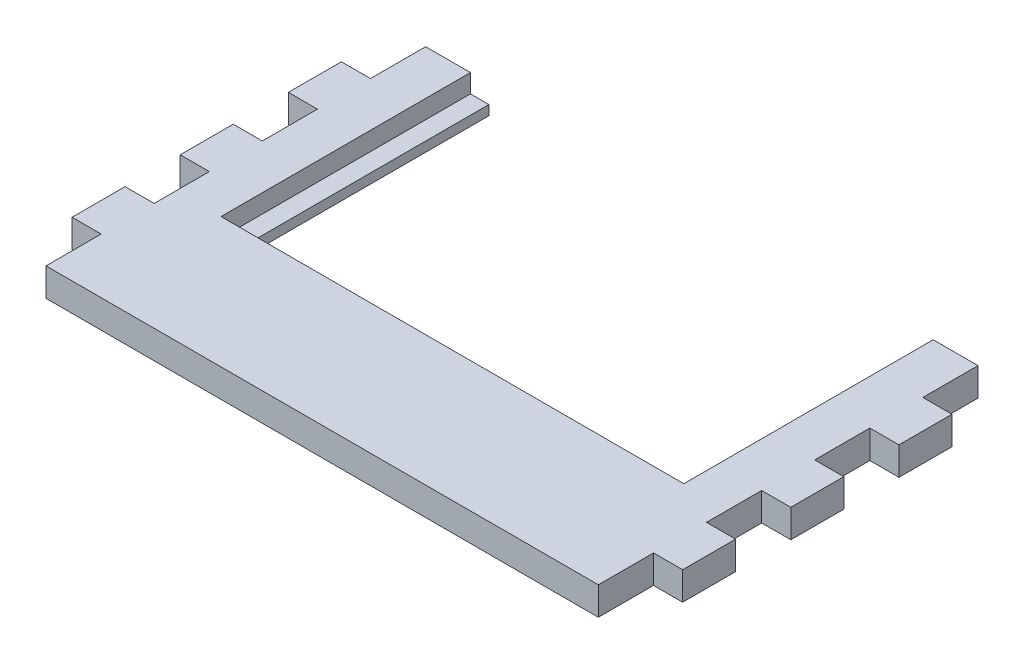
SolidWorks part; units mm, degrees
ref_plane "Plan de face" through (0, 0, 0) normal (0, 0, 1) x (1, 0, 0)
ref_plane "Plan de dessus" through (0, 0, 0) normal (0, 1, 0) x (1, 0, 0)
ref_plane "Plan de droite" through (0, 0, 0) normal (1, 0, 0) x (0, 0, -1)
sketch "Esquisse1" plane through (0, 0, 0) normal (0, 1, 0) x (1, 0, 0)
  line L1 (-163.0852, 185.3139) -> (167.4148, 185.3139)
  line L2 (-163.0852, 185.3139) -> (-163.0852, -20.1861)
  line L3 (-163.0852, -20.1861) -> (167.4148, -20.1861)
  line L4 (167.4148, 185.3139) -> (167.4148, -20.1861)
  line L5 (-113.0852, 185.3139) -> (117.4148, 185.3139)
  line L6 (-113.0852, 185.3139) -> (-113.0852, 60.3139)
  line L7 (-113.0852, 60.3139) -> (117.4148, 60.3139)
  line L8 (117.4148, 185.3139) -> (117.4148, 60.3139)
  dimension "D1" = 330.5
  dimension "D2" = 205.5
  dimension "D3" = 50
  dimension "D4" = 50
  dimension "D5" = 80.5
extrude "Boss.-Extru.1" add sketch "Esquisse1" along normal blind 15.25 contours L1 L8 L7 L6 L2 L3 L4
sketch "Esquisse2" plane through (0, 15.25, 0) normal (0, 1, 0) x (1, 0, 0)
  line L0 (-163.0852, 185.3139) -> (-113.0852, 185.3139) construction
  line L1 (-123.0852, 185.3139) -> (127.4148, 185.3139)
  line L2 (-123.0852, 185.3139) -> (-123.0852, 50.3139)
  line L3 (-123.0852, 50.3139) -> (127.4148, 50.3139)
  line L4 (127.4148, 185.3139) -> (127.4148, 50.3139)
  line L5 (2.1648, -20.1861) -> (2.1648, 185.3139) construction
  line L6 (-163.0852, -20.1861) -> (167.4148, -20.1861) construction
  line L8 (-113.0852, 185.3139) -> (-113.0852, 60.3139) construction
  line L9 (-113.0852, 60.3139) -> (117.4148, 60.3139) construction
  dimension "D1" = 10
  dimension "D2" = 10
extrude "Enlèv. mat.-Extru.1" cut sketch "Esquisse2" against normal blind 10
sketch "Esquisse3" plane through (0, 15.25, 0) normal (0, 1, 0) x (1, 0, 0)
  line L0 (-163.0852, 185.3139) -> (-163.0852, -20.1861) construction
  line L1 (-163.0852, 185.3139) -> (-147.3352, 185.3139)
  line L2 (-163.0852, 185.3139) -> (-163.0852, 155.4567)
  line L3 (-163.0852, 155.4567) -> (-147.3352, 155.4567)
  line L4 (-147.3352, 185.3139) -> (-147.3352, 155.4567)
  line L5 (-163.0852, 126.7662) -> (-147.3352, 126.7662)
  line L6 (-163.0852, 126.7662) -> (-163.0852, 96.9091)
  line L7 (-163.0852, 96.9091) -> (-147.3352, 96.9091)
  line L8 (-147.3352, 126.7662) -> (-147.3352, 96.9091)
  line L9 (-163.0852, -20.1861) -> (167.4148, -20.1861) construction
  line L10 (-163.0852, 68.2186) -> (-147.3352, 68.2186)
  line L11 (-163.0852, 68.2186) -> (-163.0852, 38.3615)
  line L12 (-163.0852, 38.3615) -> (-147.3352, 38.3615)
  line L13 (-147.3352, 68.2186) -> (-147.3352, 38.3615)
  line L14 (-163.0852, 9.671) -> (-147.3352, 9.671)
  line L15 (-163.0852, 9.671) -> (-163.0852, -20.1861)
  line L16 (-163.0852, -20.1861) -> (-147.3352, -20.1861)
  line L17 (-147.3352, 9.671) -> (-147.3352, -20.1861)
  line L18 (-163.0852, 9.671) -> (-163.0852, 38.3615) construction
  line L19 (-163.0852, 68.2186) -> (-163.0852, 96.9091) construction
  line L20 (-163.0852, 126.7662) -> (-163.0852, 155.4567) construction
  line L21 (-147.8352, 155.9567) -> (-147.8352, 185.3139) construction
  line L22 (-147.8352, 155.9567) -> (-163.0852, 155.9567) construction
  dimension "D1" = 0.5
  dimension "D2" = 0.5
extrude "Enlèv. mat.-Extru.2" cut sketch "Esquisse3" against normal up to next (15.25 mm away)
ref_plane "Plan1" through (2.1648, 0, 0) normal (-1, 0, 0) x (0, 0, 1)
mirror "Symétrie1" about plane through (2.1648, 0, 0) normal (-1, 0, 0) of "Enlèv. mat.-Extru.2"
